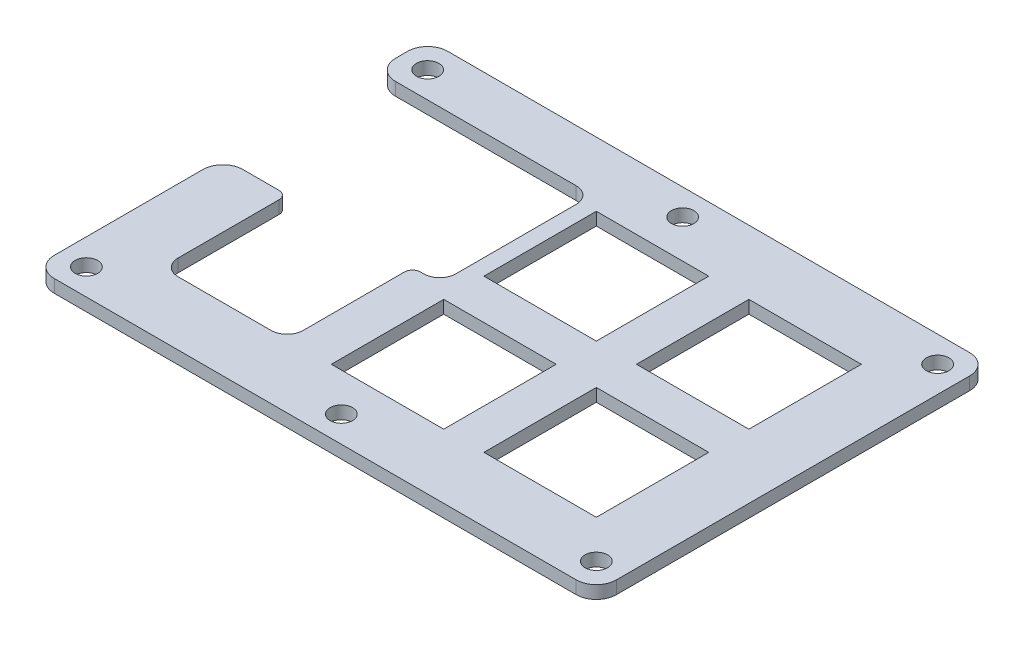
SolidWorks part; units mm, degrees
ref_plane "Front Plane" through (0, 0, 0) normal (0, 0, 1) x (1, 0, 0)
ref_plane "Top Plane" through (0, 0, 0) normal (0, 1, 0) x (1, 0, 0)
ref_plane "Right Plane" through (0, 0, 0) normal (1, 0, 0) x (0, 0, -1)
sketch "Sketch1" plane through (0, 0, 0) normal (0, 1, 0) x (1, 0, 0)
  line L1 (20, -19.5) -> (-20, -19.5)
  line L2 (20, -19.5) -> (20, 19.5)
  line L3 (20, 19.5) -> (-20, 19.5)
  line L4 (-20, -19.5) -> (-20, 19.5)
  line L5 (20, -19.5) -> (-20, 19.5) construction
  line L6 (20, 19.5) -> (-20, -19.5) construction
  point P0 (0, 0)
  dimension "D1" = 39
  dimension "D2" = 40
extrude "Boss-Extrude1" add sketch "Sketch1" along normal blind 1.6
sketch "Sketch3" plane through (0, 0, 0) normal (0, 1, 0) x (1, 0, 0)
  line L0 (25, 24.5) -> (-45, 24.5)
  line L1 (-45, 24.5) -> (-45, -24.5)
  line L2 (-45, -24.5) -> (25, -24.5)
  line L3 (25, -24.5) -> (25, 24.5)
  line L4 (20, -19.5) -> (20, 19.5) construction
  line L5 (25, 0) -> (0, 0) construction
  dimension "D1" = 70
  dimension "D2" = 49
  dimension "D3" = 5
extrude "Boss-Extrude2" add sketch "Sketch3" along normal up to surface (1.6 mm away) up to face at (0, 1.6, 0)
sketch "Sketch4" plane through (0, 1.6, 0) normal (0, 1, 0) x (1, 0, 0)
  line L0 (25, 24.5) -> (-45, 24.5) construction
  line L1 (-45, 18) -> (-18, 18)
  line L2 (-45, 18) -> (-45, -1)
  line L3 (-45, -1) -> (-18, -1)
  line L4 (-18, 18) -> (-18, -1)
  line L5 (-45, 18) -> (-18, -1) construction
  line L6 (-10, 24.5) -> (-10, -24.5) construction
  line L7 (-45, -24.5) -> (25, -24.5) construction
  line L8 (-45, 24.5) -> (-45, -24.5) construction
  point P6 (-31.5, 8.5)
  point P8 (-38.5, 19.4198)
  dimension "D1" = 27
  dimension "D2" = 19
  dimension "D4" = 8.5
extrude "Cut-Extrude1" cut sketch "Sketch4" against normal through all
fillet "Fillet1" radius 2 2 edges at (-18, 0.8, 1) (-18, 0.8, -18)
sketch "Sketch5" plane through (0, 1.6, 0) normal (0, 1, 0) x (1, 0, 0)
  line L1 (-37, -1) -> (-21.4, -1)
  line L2 (-37, -1) -> (-37, -16.6)
  line L3 (-37, -16.6) -> (-21.4, -16.6)
  line L4 (-21.4, -1) -> (-21.4, -16.6)
  line L5 (-37, -1) -> (-21.4, -16.6) construction
  line L6 (-10, -24.5) -> (-10, 24.5) construction
  line L7 (-45, -24.5) -> (25, -24.5) construction
  line L8 (25, 24.5) -> (-45, 24.5) construction
  line L9 (-45, -1) -> (-20, -1) construction
  point P6 (-29.2, -8.8)
  dimension "D1" = 15.6
  dimension "D2" = 19.2
  dimension "D3" = 16.6
extrude "Cut-Extrude2" cut sketch "Sketch5" against normal through all
fillet "Fillet2" radius 2 2 edges at (-37, 0.8, 16.6) (-21.4, 0.8, 16.6)
fillet "Fillet3" radius 1 2 edges at (-21.4, 0.8, 1) (-37, 0.8, 1)
sketch "Sketch6" plane through (0, 1.6, 0) normal (0, 1, 0) x (1, 0, 0)
  line L0 (-45, 24.5) -> (-45, 18) construction
  line L1 (-41.75, 21.25) -> (21.75, 21.25) construction
  line L2 (-41.75, 21.25) -> (-41.75, -21.25) construction
  line L3 (-41.75, -21.25) -> (21.75, -21.25) construction
  line L4 (21.75, 21.25) -> (21.75, -21.25) construction
  line L5 (25, -24.5) -> (25, 24.5) construction
  line L6 (-45, -24.5) -> (25, -24.5) construction
  line L7 (25, 24.5) -> (-45, 24.5) construction
  line L8 (-10, 21.25) -> (-10, -21.25) construction
  line L9 (-41.75, 0) -> (-10, 0) construction
  line L10 (-10, 0) -> (21.75, 0) construction
  circle A0 centre (-41.75, 21.25) radius 1.4
  circle A1 centre (21.75, 21.25) radius 1.4
  circle A2 centre (21.75, -21.25) radius 1.4
  circle A3 centre (-41.75, -21.25) radius 1.4
  circle A4 centre (-10, -21.25) radius 1.4
  circle A5 centre (-10, 21.25) radius 1.4
  dimension "D5" = 2.8
  dimension "D1" = 3.25
  dimension "D2" = 3.25
  dimension "D3" = 3.25
  dimension "D4" = 3.25
  dimension "D6" = 42.5
extrude "Cut-Extrude3" cut sketch "Sketch6" against normal through all
fillet "Fillet4" radius 2.5 6 edges at (25, 0.8, -24.5) (-45, 0.8, 24.5) (-45, 0.8, -24.5) (25, 0.8, 24.5) (-45, 0.8, 1) (-45, 0.8, -18)
sketch "Sketch7" plane through (0, 1.6, 0) normal (0, 1, 0) x (1, 0, 0)
  line L0 (-44.2678, -23.7678) -> (24.2678, 23.7678) construction
  line L1 (-16, 16.5) -> (-2, 16.5)
  line L2 (-16, 16.5) -> (-16, 2.5)
  line L3 (-16, 2.5) -> (-2, 2.5)
  line L4 (-2, 16.5) -> (-2, 2.5)
  line L5 (-16, 16.5) -> (-2, 2.5) construction
  line L6 (-16, 2.5) -> (-2, 16.5) construction
  arc A0 (-45, -22) -> (-42.5, -24.5) centre (-42.5, -22) ccw construction
  arc A1 (25, 22) -> (22.5, 24.5) centre (22.5, 22) ccw construction
  point P0 (-9, 9.5)
  point P13 (-10, 0)
  dimension "D1" = 1
  dimension "D2" = 9.5
  dimension "D3" = 14
  dimension "D4" = 14
extrude "Cut-Extrude4" cut sketch "Sketch7" against normal through all
pattern_linear "LPattern1" count 2 spacing 19 along (1, 0, 0) count 2 spacing 19 along (0, 0, 1) of "Cut-Extrude4"
